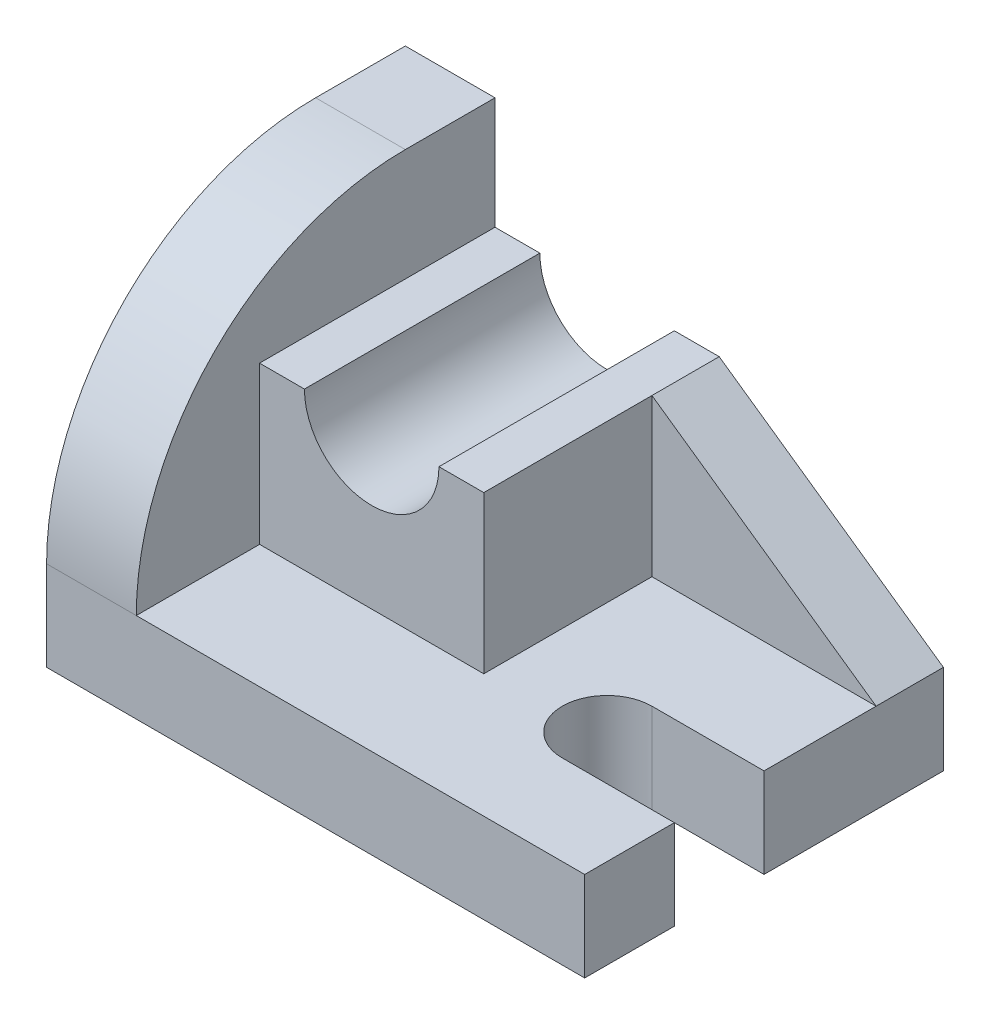
SolidWorks part; units mm, degrees
ref_plane "Front Plane" through (0, 0, 0) normal (0, 0, 1) x (1, 0, 0)
ref_plane "Top Plane" through (0, 0, 0) normal (0, 1, 0) x (1, 0, 0)
ref_plane "Right Plane" through (0, 0, 0) normal (1, 0, 0) x (0, 0, -1)
sketch "Sketch1" plane through (0, 0, 0) normal (0, 1, 0) x (1, 0, 0)
  line L1 (-48, 32) -> (48, 32)
  line L2 (-48, 32) -> (-48, -32)
  line L3 (-48, -32) -> (48, -32)
  line L4 (48, 32) -> (48, -32)
  line L5 (-48, 32) -> (48, -32) construction
  line L6 (-48, -32) -> (48, 32) construction
  point P0 (0, 0)
  dimension "D1" = 96
  dimension "D2" = 64
extrude "Boss-Extrude1" add sketch "Sketch1" along normal blind 16
sketch "Sketch2" plane through (0, 16, 0) normal (0, 1, 0) x (1, 0, 0)
  line L0 (-48, -32) -> (48, -32) construction
  line L1 (-48, 32) -> (-32, 32)
  line L2 (-48, 32) -> (-48, -32)
  line L3 (-48, -32) -> (-32, -32)
  line L4 (-32, 32) -> (-32, -32)
  dimension "D1" = 16
extrude "Boss-Extrude2" add sketch "Sketch2" along normal blind 48 contours L2 L1 L4 L3
fillet "Fillet3" radius 48 1 edges at (-40, 64, 32)
sketch "Sketch3" plane through (0, 16, 0) normal (0, 1, 0) x (1, 0, 0)
  line L1 (-32, 32) -> (8, 32)
  line L2 (-32, 32) -> (-32, -10)
  line L3 (-32, -10) -> (8, -10)
  line L4 (8, 32) -> (8, -10)
  dimension "D1" = 40
  dimension "D2" = 42
extrude "Boss-Extrude3" add sketch "Sketch3" along normal blind 28 contours L2 L1 L4 L3
sketch "Sketch4" plane through (0, 0, 10) normal (0, 0, 1) x (1, 0, 0)
  line L0 (-32, 44) -> (8, 44) construction
  circle A0 centre (-12, 44) radius 12
  dimension "D1" = 24
extrude "Cut-Extrude1" cut sketch "Sketch4" against normal through all contours A0
sketch "Sketch5" plane through (0, 0, -32) normal (0, 0, -1) x (-1, 0, 0)
  line L0 (-8, 16) -> (-8, 44)
  line L1 (-8, 44) -> (-48, 16)
  line L2 (-48, 16) -> (-8, 16)
extrude "Boss-Extrude4" add sketch "Sketch5" against normal blind 12
sketch "Sketch6" plane through (0, 16, 0) normal (0, 1, 0) x (1, 0, 0)
  line L0 (28, -8) -> (48, -8) construction
  line L1 (48, -32) -> (48, 20) construction
  line L2 (28, 0) -> (48, 0)
  line L3 (28, -16) -> (48, -16)
  line L4 (-32, -32) -> (48, -32) construction
  arc A0 (28, 0) -> (28, -16) centre (28, -8) ccw
  arc A1 (48, -16) -> (48, 0) centre (48, -8) ccw
  point P4 (38, -8)
  dimension "D1" = 16
  dimension "D2" = 20
  dimension "D3" = 16
extrude "Cut-Extrude2" cut sketch "Sketch6" against normal through all
